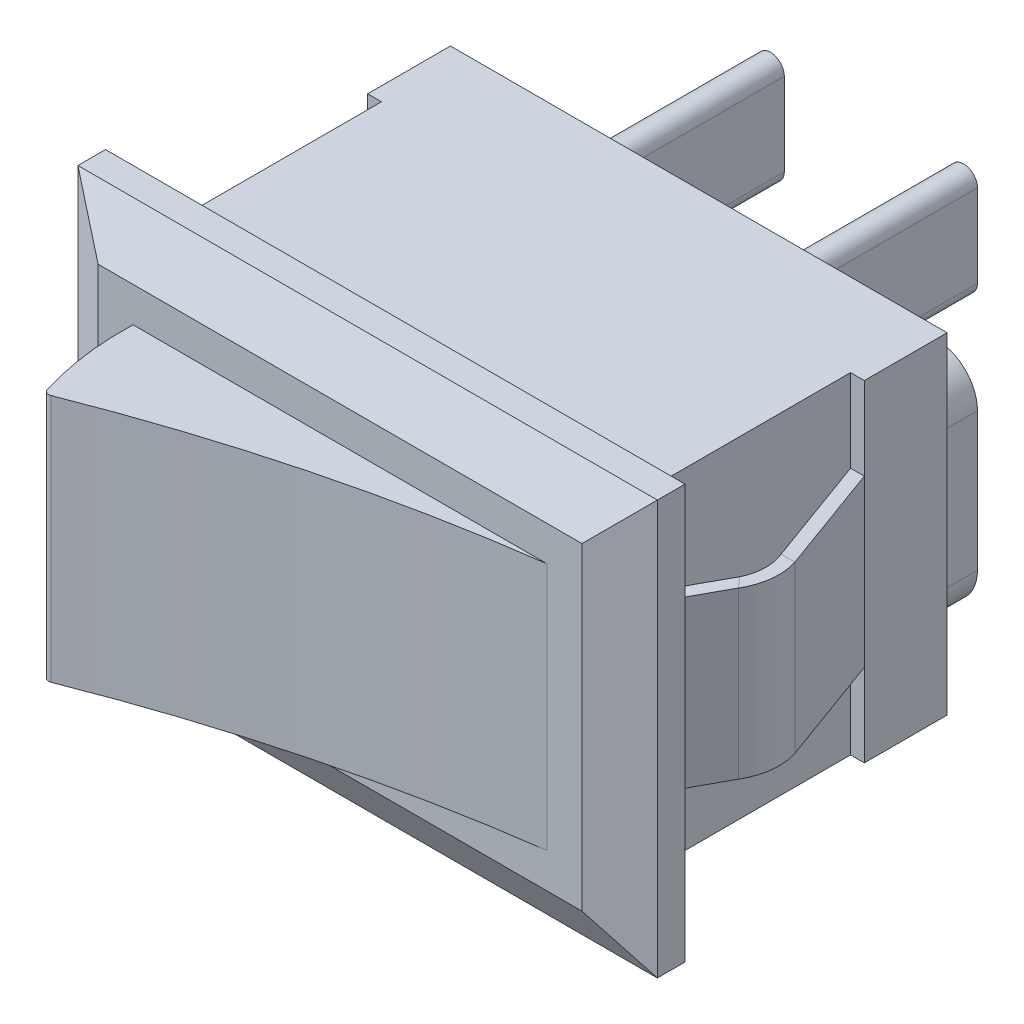
SolidWorks part; units mm, degrees
ref_plane "前视基准面" through (0, 0, 0) normal (0, 0, 1) x (1, 0, 0)
ref_plane "上视基准面" through (0, 0, 0) normal (0, 1, 0) x (1, 0, 0)
ref_plane "右视基准面" through (0, 0, 0) normal (1, 0, 0) x (0, 0, -1)
sketch "草图1" plane through (0, 0, 0) normal (0, 0, 1) x (1, 0, 0)
  line L1 (0, 0) -> (21, 0)
  line L2 (0, 0) -> (0, 15)
  line L3 (0, 15) -> (21, 15)
  line L4 (21, 0) -> (21, 15)
  dimension "D1" = 21
  dimension "D2" = 15
extrude "凸台-拉伸1" add sketch "草图1" along normal blind 17
sketch "草图3" plane through (0, 0, 0) normal (0, 0, -1) x (-1, 0, 0)
  line L8 (-1.5, 1.5) -> (-1.5, 13.5)
  line L9 (-1.5, 13.5) -> (-19.5, 13.5)
  line L10 (-19.5, 13.5) -> (-19.5, 1.5)
  line L11 (-19.5, 1.5) -> (-1.5, 1.5)
  line L12 (-1.5, 1.5) -> (-1.5, 13.5)
  line L13 (-1.5, 13.5) -> (-19.5, 13.5)
  line L14 (-19.5, 13.5) -> (-19.5, 1.5)
  line L15 (-19.5, 1.5) -> (-1.5, 1.5)
  dimension "D1" = 1.5
extrude "切除-拉伸1" cut sketch "草图3" against normal blind 11 flip side to cut
sketch "草图4" plane through (0, 0, 17) normal (0, 0, 1) x (1, 0, 0)
  line L0 (0, 7.5) -> (21, 7.5) construction
  line L1 (0, 15) -> (0, 0) construction
  line L2 (21, 0) -> (21, 15) construction
  line L3 (10.5, 15) -> (10.5, 0) construction
  line L4 (21, 15) -> (0, 15) construction
  line L5 (0, 0) -> (21, 0) construction
  line L7 (3, 12) -> (18, 12)
  line L8 (3, 12) -> (3, 3)
  line L9 (3, 3) -> (18, 3)
  line L10 (18, 12) -> (18, 3)
  line L11 (3, 12) -> (18, 3) construction
  line L12 (3, 3) -> (18, 12) construction
  point P12 (10.5, 7.5)
  dimension "D1" = 15
  dimension "D2" = 9
extrude "切除-拉伸2" cut sketch "草图4" against normal blind 4 flip side to cut
sketch "草图5" plane through (0, 3, 0) normal (0, -1, 0) x (1, 0, 0)
  line L0 (0, 13) -> (21, 13) construction
  line L1 (18, 13) -> (18, 17) construction
  line L2 (3, 17) -> (3.7861, 18.9267)
  line L3 (3.7861, 18.9267) -> (19.848, 18.6434)
  line L4 (19.848, 18.6434) -> (18, 13)
  arc A0 (3, 17) -> (18, 13) centre (26.1906, 73.8398) ccw
extrude "切除-拉伸3" cut sketch "草图5" against normal up to next
sketch "草图6" plane through (0, 3, 0) normal (0, -1, 0) x (1, 0, 0)
  line L0 (3.5387, 16.7832) -> (1.8345, 18.2595)
  line L1 (1.8345, 18.2595) -> (1.8345, 13.5458)
  line L2 (1.8345, 13.5458) -> (3, 13)
  arc A0 (3, 13) -> (3.5387, 16.7832) centre (13.8882, 13.3795) cw
  arc A1 (3, 17) -> (18, 13) centre (26.1906, 73.8398) ccw construction
extrude "切除-拉伸4" cut sketch "草图6" against normal up to next
fillet "圆角2" radius 0.2 1 edges at (3.5387, 7.5, 16.7832)
chamfer "倒角1" distance 1 angle 60 4 edges at (10.5, 15, 13) (21, 7.5, 13) (0, 7.5, 13) (10.5, 0, 13)
sketch "草图7" plane through (0, 1.5, 0) normal (0, -1, 0) x (1, 0, 0)
  line L0 (-1.2154, 3) -> (2, 3)
  line L1 (2, 3) -> (2, 11)
  line L2 (21, 11) -> (0, 11) construction
  line L3 (2, 11) -> (-1.2154, 11)
  line L4 (-1.2154, 11) -> (-1.2154, 3)
  line L5 (19.5, 0) -> (1.5, 0) construction
  line L6 (1.5, 11) -> (1.5, 0) construction
  line L7 (10.5, 11) -> (10.5, 0) construction
  line L8 (19, 3) -> (19, 11)
  line L9 (22.2154, 3) -> (19, 3)
  line L10 (19, 11) -> (22.2154, 11)
  line L11 (22.2154, 11) -> (22.2154, 3)
  dimension "D1" = 3
  dimension "D2" = 0.5
extrude "切除-拉伸5" cut sketch "草图7" against normal up to next
sketch "草图8" plane through (0, 0, 3) normal (0, 0, 1) x (1, 0, 0)
  line L0 (1.75, 13.5) -> (1.75, 1.5) construction
  line L1 (1.5, 13.5) -> (2, 13.5) construction
  line L2 (1.5, 1.5) -> (2, 1.5) construction
  line L3 (1.5, 7.5) -> (3.4272, 7.5) construction
  line L4 (1.5, 1.5) -> (1.5, 13.5) construction
  line L6 (2, 4.5) -> (1.5, 4.5)
  line L7 (2, 4.5) -> (2, 10.5)
  line L8 (2, 10.5) -> (1.5, 10.5)
  line L9 (1.5, 4.5) -> (1.5, 10.5)
  line L10 (2, 4.5) -> (1.5, 10.5) construction
  line L11 (2, 10.5) -> (1.5, 4.5) construction
  point P10 (1.75, 7.5)
  point P15 (1.75, 4.5)
  dimension "D1" = 6
ref_plane "基准面1" through (0, 7.5, 0) normal (0, -1, 0) x (-1, 0, 0)
sketch "草图9" plane through (0, 7.5, 0) normal (0, -1, 0) x (-1, 0, 0)
  line L0 (-1.75, -3) -> (-0.3098, -6.9569)
  line L1 (0, -11) -> (0, -2.4096) construction
  line L2 (-2, -3) -> (-2, -11) construction
  line L3 (-0.4355, -8.6024) -> (-1.75, -11)
  line L4 (-21, -11) -> (0, -11) construction
  arc A0 (-0.4355, -8.6024) -> (-0.3098, -6.9569) centre (-2.1892, -7.6409) ccw
  point P15 (0, -7.8081)
  dimension "D2" = 2
  dimension "D1" = 20
sweep "扫描1" add profiles "草图8" path "草图9"
ref_plane "基准面2" through (10.5, 0, 0) normal (1, 0, 0) x (0, 0, -1)
mirror "镜向1" about plane through (10.5, 0, 0) normal (1, 0, 0) of "扫描1"
sketch "草图10" plane through (0, 0, 0) normal (0, 0, -1) x (-1, 0, 0)
  line L0 (-19.5, 7.5) -> (-1.5, 7.5) construction
  line L1 (-19.5, 13.5) -> (-19.5, 1.5) construction
  line L2 (-1.5, 1.5) -> (-1.5, 13.5) construction
  line L3 (-10.5, 13.5) -> (-10.5, 0) construction
  line L4 (-1.5, 13.5) -> (-19.5, 13.5) construction
  line L5 (-21, 0) -> (0, 0) construction
  line L6 (-3.5, 5) -> (-3.5, 10) construction
  line L7 (-5, 5) -> (-5, 10)
  line L8 (-2, 5) -> (-2, 10)
  arc A0 (-5, 5) -> (-2, 5) centre (-3.5, 5) ccw
  arc A1 (-2, 10) -> (-5, 10) centre (-3.5, 10) ccw
  point P14 (-3.5, 7.5)
  dimension "D1" = 1.5
  dimension "D2" = 5
  dimension "D3" = 7
extrude "凸台-拉伸2" add sketch "草图10" along normal blind 1.6
sketch "草图11" plane through (0, 0, -1.6) normal (0, 0, -1) x (-1, 0, 0)
  line L0 (-3.5, 11.5) -> (-3.5, 3.5) construction
  line L1 (-3.5, 6) -> (-3.5, 9) construction
  line L2 (-4, 6) -> (-4, 9)
  line L3 (-3, 6) -> (-3, 9)
  arc A0 (-2, 10) -> (-5, 10) centre (-3.5, 10) ccw construction
  arc A1 (-5, 5) -> (-2, 5) centre (-3.5, 5) ccw construction
  arc A2 (-4, 6) -> (-3, 6) centre (-3.5, 6) ccw
  arc A3 (-3, 9) -> (-4, 9) centre (-3.5, 9) ccw
  point P10 (-3.5, 7.5)
  dimension "D1" = 0.5
  dimension "D2" = 3
extrude "凸台-拉伸3" add sketch "草图11" along normal blind 8
pattern_linear "阵列(线性)2" count 3 spacing 7 along (1, 0, 0) of "凸台-拉伸2"
pattern_linear "阵列(线性)3" count 2 spacing 7 along (1, 0, 0) of "凸台-拉伸3"
